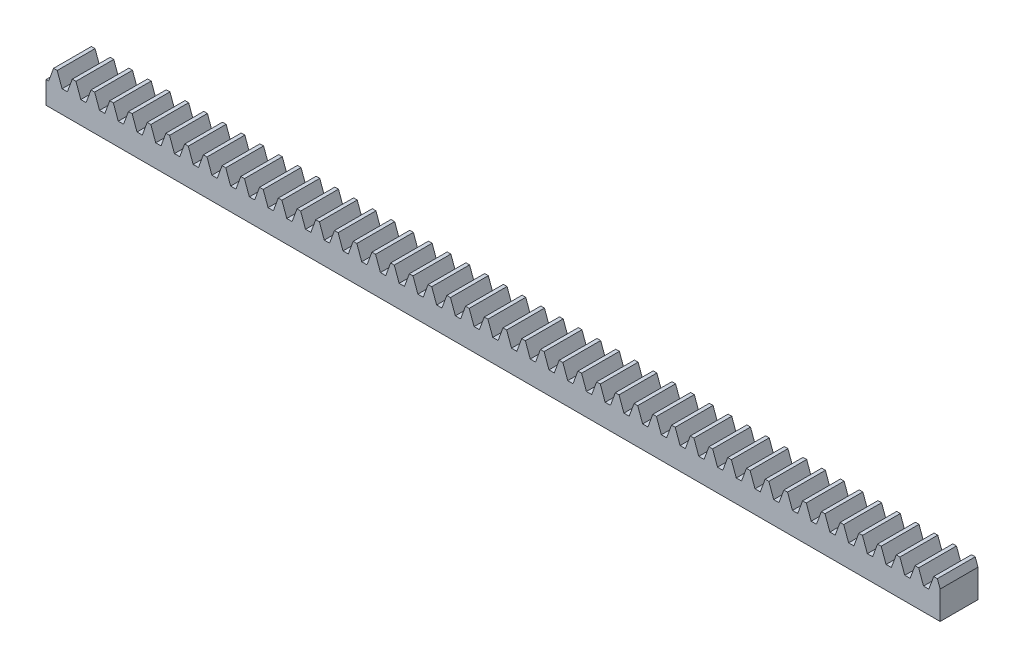
SolidWorks part; units mm, degrees
ref_plane "Plane1" through (0, 0, 0) normal (0, 0, 1) x (1, 0, 0)
ref_plane "Plane2" through (0, 0, 0) normal (0, 1, 0) x (1, 0, 0)
ref_plane "Plane3" through (0, 0, 0) normal (1, 0, 0) x (0, 0, -1)
sketch "HoldingSke" plane through (0, 0, 0) normal (0, 1, 0) x (1, 0, 0)
  line L0 (0, 0) -> (0.1392, 0.9903)
  line L1 (-15, 0) -> (100, 0) construction
  line L2 (0, 0) -> (-2.1039, 2.3779)
  line L3 (0, 0) -> (-11.863, 4.5341)
  line L4 (0, 0) -> (5.6657, 6.5177)
  line L5 (0, 0) -> (-23.7986, -8.8762)
  line L6 (0, 0) -> (-10.5278, -7.1032)
  line L9 (-71.009, 38.7566) -> (69.9449, 90.0596)
  line L10 (-76.2, 3.3779) -> (-71.2, 3.3779)
  line L11 (0, 0) -> (-6.35, 0)
  line L12 (-76.2, 101.6) -> (-76.162, 101.6)
  line L13 (24.9733, 27.94) -> (52.9518, 28.4284)
  line L14 (24.9733, 27.94) -> (24.9743, 27.94)
  line L15 (24.9733, 27.94) -> (100.4006, 29.5858)
  circle A0 centre (0, 0) radius 19.05
  circle A1 centre (0, 0) radius 2.5
  circle A2 centre (0, 0) radius 12.7
  dimension "MPH" = 5
  dimension "Diameter" = 38.1
  dimension "Num_teeth" = 49
  dimension "Pitch" = 1
  dimension "Width" = 6.35
  dimension "Show_teeth" = 998
  dimension "Thickness" = 12.7
  dimension "Ap" = 20
  dimension "Pitch_height" = 5
  dimension "Backlash" = 0.038
  dimension "Addendum_fac" = 1
  dimension "Dedendum_fac" = 1.25
  dimension "Clearance_fac" = 0.25
  dimension "Dedendum_add" = 0.001
  dimension "Length" = 150
  dimension "Module" = 1
sketch "BlankSke" plane through (0, 0, 0) normal (0, 0, 1) x (1, 0, 0)
  line L1 (0, 0) -> (150, 0)
  line L2 (0, 0) -> (0, 6)
  line L3 (0, 6) -> (150, 6)
  line L4 (150, 0) -> (150, 6)
  dimension "Length" = 150
  dimension "Blank_height" = 6
extrude "Blank" add sketch "BlankSke" against normal blind 6.35
sketch "TooCutSkeIll" plane through (0, 0, 0) normal (0, 0, 1) x (1, 0, 0)
  line L0 (-1.2538, 5.9737) -> (-0.5045, 3.9152)
  line L1 (-0.2687, 3.75) -> (0.2687, 3.75)
  line L2 (0.5045, 3.9152) -> (1.2538, 5.9737)
  line L3 (150, 6) -> (0, 6) construction
  line L4 (0, 0) -> (0, 64.897) construction
  line L5 (-13.208, 5) -> (12.954, 5) construction
  line L6 (0, 0) -> (150, 0) construction
  line L7 (0.8994, 5) -> (0.8994, 48.7463) construction
  line L8 (-0.8994, 5) -> (-0.8994, 48.7463) construction
  line L9 (1.2914, 6) -> (1.2914, 6.0254)
  line L10 (-1.2914, 6) -> (-1.2914, 6.0254)
  line L11 (-1.2914, 6.0254) -> (1.2914, 6.0254)
  arc A0 (0.2687, 3.75) -> (0.5045, 3.9152) centre (0.2687, 4.001) ccw
  arc A1 (-0.5045, 3.9152) -> (-0.2687, 3.75) centre (-0.2687, 4.001) ccw
  arc A2 (1.2914, 6) -> (1.2538, 5.9737) centre (1.2914, 5.96) ccw
  arc A3 (-1.2538, 5.9737) -> (-1.2914, 6) centre (-1.2914, 5.96) ccw
  dimension "Root_fillet" = 0.251
  dimension "Break_rad" = 0.04
  dimension "Pitch_height" = 5
  dimension "Gap_width" = 1.7988
  dimension "Dedendum" = 1.25
  dimension "Addendum_plus" = 1.0254
  dimension "Pressure_angle" = 20
extrude "ToothCutIll" [suppressed] cut sketch "TooCutSkeIll" against normal through all
sketch "TooCutSkeSim" plane through (0, 0, 0) normal (0, 0, 1) x (1, 0, 0)
  line L0 (0.4444, 3.75) -> (-0.4444, 3.75)
  line L1 (1.2726, 6.0254) -> (0.4444, 3.75)
  line L2 (0, 17.4625) -> (0, 53.467) construction
  line L3 (1.2726, 6.0254) -> (-1.2726, 6.0254)
  line L6 (-1.2726, 6.0254) -> (-0.4444, 3.75)
  line L9 (-0.8994, 5) -> (0.8994, 5) construction
  line L10 (0, 0) -> (150, 0) construction
  line L11 (0.8994, 5) -> (0.8994, 53.467) construction
  line L12 (-0.8994, 5) -> (-0.8994, 53.467) construction
  dimension "Pitch_height" = 5
  dimension "Pressure_angle" = 20
  dimension "Gap_width" = 1.7988
  dimension "Dedendum" = 1.25
  dimension "Addendum_plus" = 1.0254
extrude "ToothCutSim" cut sketch "TooCutSkeSim" against normal through all
pattern_linear "TeethCuts" count 48 spacing 3.1416 along (1, 0, 0) of "ToothCutIll", "ToothCutSim"
equation "' \"Module@HoldingSke\" = 6.35"
equation "' \"Num_teeth@HoldingSke\" = 12"
equation "' \"Ap@HoldingSke\" =  20"
equation "' \"Width@HoldingSke\" = 0.25 * 25.4"
equation "' \"Show_teeth@HoldingSke\" = 500"
equation "' \"Backlash@HoldingSke\" = 0.009 * 25.4"
equation "' \"Addendum_fac@HoldingSke\" = 1.0"
equation "' \"Dedendum_fac@HoldingSke\" = 1.25"
equation "' \"Dedendum_add@HoldingSke\" = 0.00005 * 25.4"
equation "' \"Clearance_fac@HoldingSke\" = 0.25"
equation "' \"Pitch_height@HoldingSke\" = 1 * 25.4"
equation "' \"Length@HoldingSke\" = 4.71 * 25.4"
equation "\"Pitch@HoldingSke\" = 1 / \"Module@HoldingSke\""
equation "\"MPH@HoldingSke\" = \"Dedendum_fac@HoldingSke\" / \"Pitch@HoldingSke\" + 2 * \"Dedendum_add@HoldingSke\" + 0.002 * 25.4"
equation "\"MPH@HoldingSke\" = ((sgn( \"MPH@HoldingSke\" - \"Pitch_height@HoldingSke\")+1)*( \"MPH@HoldingSke\" - \"Pitch_height@HoldingSke\"))/2 + \"Pitch_height@HoldingSke\""
equation "\"Blank_height@BlankSke\" = \"Pitch_height@HoldingSke\" + \"Addendum_fac@HoldingSke\"  / \"Pitch@HoldingSke\" "
equation "\"Length@BlankSke\" =  \"Length@HoldingSke\""
equation "\"Face_width@Blank\" = \"Width@HoldingSke\""
equation "\"Pressure_angle@TooCutSkeIll\" = \"Ap@HoldingSke\""
equation "\"Addendum_plus@TooCutSkeIll\" =  \"Addendum_fac@HoldingSke\"  / \"Pitch@HoldingSke\" + 0.001 *25.4"
equation "\"Dedendum@TooCutSkeIll\" = \"Dedendum_fac@HoldingSke\"  / \"Pitch@HoldingSke\""
equation "\"Pitch_height@TooCutSkeIll\" =  \"MPH@HoldingSke\""
equation "\"Gap_width@TooCutSkeIll\" = 3.14159265 / 2 / \"Pitch@HoldingSke\" + 6 * \"Backlash@HoldingSke\""
equation "\"Pressure_angle@TooCutSkeSim\" = \"Ap@HoldingSke\""
equation "\"Addendum_plus@TooCutSkeSim\" =  \"Addendum_fac@HoldingSke\"  / \"Pitch@HoldingSke\" + 0.001 * 25.4"
equation "\"Dedendum@TooCutSkeSim\" = \"Dedendum_fac@HoldingSke\"  / \"Pitch@HoldingSke\""
equation "\"Pitch_height@TooCutSkeSim\" =  \"MPH@HoldingSke\""
equation "\"Gap_width@TooCutSkeSim\" = 3.14159265 / 2 / \"Pitch@HoldingSke\" + 6 * \"Backlash@HoldingSke\""
equation "\"Root_fillet@TooCutSkeIll\" = \"Clearance_fac@HoldingSke\" / \"Pitch@HoldingSke\" + \"Dedendum_add@HoldingSke\""
equation "\"Break_rad@TooCutSkeIll\" = 0.02 / \"Pitch@HoldingSke\" * 2"
equation "\"Linear_pitch@TeethCuts\" = 3.14159265 / \"Pitch@HoldingSke\""
equation "\"Num_teeth@HoldingSke\" = int( ( \"Length@HoldingSke\" + 0 ) / (3.14159265 / \"Pitch@HoldingSke\")) + 0.9999  + 1"
equation " \"Num_teeth@TeethCuts\" = int( \"Show_teeth@HoldingSke\" ) + 1"
equation " \"Num_teeth@TeethCuts\" = ((sgn( \"Num_teeth@TeethCuts\" - \"Num_teeth@HoldingSke\" )-1)*( \"Num_teeth@TeethCuts\" - \"Num_teeth@HoldingSke\" ))/-2+ \"Num_teeth@HoldingSke\""
equation " \"Num_teeth@TeethCuts\" = ((sgn( \"Num_teeth@TeethCuts\" - 2.0)+1)*( \"Num_teeth@TeethCuts\" - 2.0))/2 +2.0"
